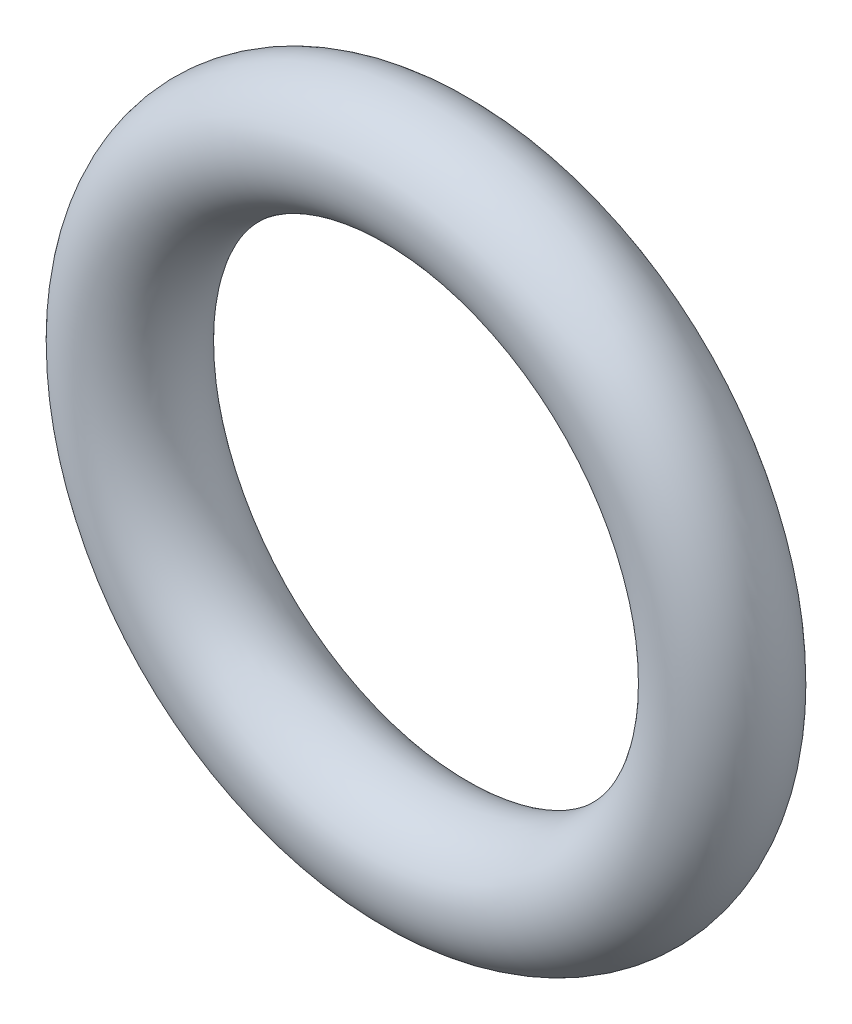
SolidWorks part; units mm, degrees
material "Rubber"
ref_plane "Front" through (0, 0, 0) normal (0, 0, 1) x (1, 0, 0)
ref_plane "Top" through (0, 0, 0) normal (0, 1, 0) x (1, 0, 0)
ref_plane "Right" through (0, 0, 0) normal (1, 0, 0) x (0, 0, -1)
sketch "Sketch1" plane through (0, 0, 0) normal (1, 0, 0) x (0, -1, 0)
  line L0 (0, -2) -> (0, 2) construction
  line L2 (-12.65, 0) -> (12.65, 0) construction
  line L3 (-8, 0) -> (8, 0) construction
  circle A0 centre (10, 0) radius 2
  point P9 (8, 0)
  point P10 (12, 0)
  point P13 (10, 2)
  point P14 (10, -2)
  dimension "Width" = 4
  dimension "ID" = 16
revolve "Revolve1" add sketch "Sketch1" angle 360 about L0
